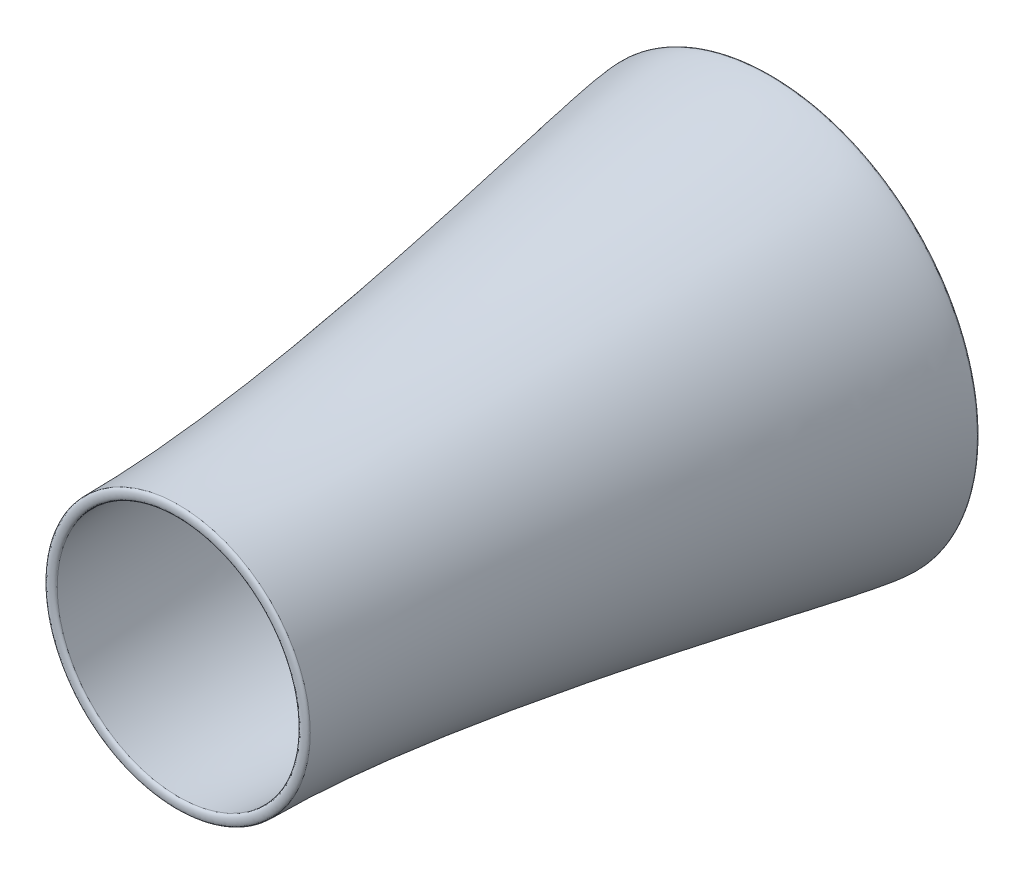
SolidWorks part; units mm, degrees
ref_plane "Front Plane" through (0, 0, 0) normal (0, 0, 1) x (1, 0, 0)
ref_plane "Top Plane" through (0, 0, 0) normal (0, 1, 0) x (1, 0, 0)
ref_plane "Right Plane" through (0, 0, 0) normal (1, 0, 0) x (0, 0, -1)
sketch "Sketch1" plane through (0, 0, 0) normal (0, 0, 1) x (1, 0, 0)
  circle A0 centre (0, 0) radius 50.8
  dimension "D1" = 101.6
ref_plane "Plane1" through (0, -254, 0) normal (0, 1, 0) x (1, 0, 0)
sketch "Sketch6" plane through (0, 0, 0) normal (0, 1, 0) x (1, 0, 0)
  line L0 (0, -99.6848) -> (0, 145.6048) construction
ref_plane "Plane2" through (0, -114.3, 0) normal (0, 1, 0) x (1, 0, 0)
sketch "Sketch12" plane through (0, 0, 0) normal (0, 1, 0) x (1, 0, 0)
  line L0 (0, -1104.7568) -> (0, -908.6135) construction
ref_plane "Plane3" through (0, 0, 203.2) normal (0, 0, 1) x (1, 0, 0)
ref_plane "Plane4" through (0, 0, 889) normal (0, 0, 1) x (1, 0, 0)
sketch "Sketch17" plane through (0, 0, 0) normal (0, 1, 0) x (1, 0, 0)
  line L0 (-259.4955, -43.5301) -> (-259.4955, 70.1436) construction
  line L1 (-110.6437, -1316.1124) -> (-110.6437, -853.5386) construction
  line L2 (-259.4955, 45.4622) -> (-387.328, 45.4622)
  line L3 (-387.328, 45.4622) -> (-387.328, -1084.8928)
  line L4 (-387.328, -1084.8928) -> (-110.6437, -1084.8928)
  spline S0 degree 3 poles (-259.4955, 45.4622) (-259.4955, -7.1736) (-207.7477, -105.8122) (-173.3147, -383.1384) (-92.4228, -818.9689) (-110.6437, -795.7842) (-110.6437, -1084.8928) knots 0 0 0 0 0.158009 0.206507 0.484977 1 1 1 1
sketch "Sketch21" plane through (0, 0, 0) normal (0, 1, 0) x (1, 0, 0)
  line L0 (-711.6099, -22.8536) -> (-711.6099, 113.778) construction
  line L1 (-450.1433, -1315.9117) -> (-450.1433, -853.874) construction
  line L2 (-622.1484, -0.8938) -> (-711.6099, -0.8938) construction
  line L3 (-414.4897, -2018.6594) -> (-450.1433, -2018.6594) construction
  line L4 (-414.4897, -2018.6594) -> (-450.1433, -2018.6594)
  line L6 (-622.1484, -0.8938) -> (-711.6099, -0.8938)
  spline S0 degree 3 poles (-622.1484, -0.8938) (-512.5874, -283.5588) (-414.9729, -786.3752) (-442.509, -1553.9603) (-414.4897, -2018.6594) knots 0 0 0 0 0.206507 1 1 1 1
  spline S1 degree 3 poles (-711.6099, -0.8938) (-711.6099, -126.2777) (-450.1433, -1288.3503) (-450.1433, -2018.6594) knots 0 0 0 0 1 1 1 1
  point P10 (-490.7044, -494.9814)
  point P11 (-570.9986, -443.7774)
  point P12 (-450.1433, -1074.8673)
  point P13 (-462.4277, -423.8357)
  point P14 (-385.8107, -2020.9984)
  point P15 (-441.2042, -1016.4054)
  point P16 (-414.4897, -2018.6594)
  point P17 (-484.9125, -450.8925)
revolve "Revolve2" add sketch "Sketch21" angle 360 about L0
sketch "Sketch22" plane through (0, 0, 0) normal (0, 1, 0) x (1, 0, 0)
  line L0 (-711.6099, -0.8938) -> (-622.1484, -0.8938)
  line L1 (-622.1484, -4.7028) -> (-622.1484, 2.9153) construction
  line L2 (-711.6099, 0.499) -> (-711.6099, -2.2865) construction
  spline S0 degree 3 poles (-711.6099, -0.8938) (-711.6099, 16.0396) (-622.1484, 16.0396) (-622.1484, -0.8938) knots 0 0 0 0 1 1 1 1
revolve "Revolve3" add sketch "Sketch22" angle 360 about L0
sketch "Sketch23" plane through (0, 0, 0) normal (0, 1, 0) x (1, 0, 0)
  line L0 (-450.1433, -2018.6594) -> (-414.4897, -2018.6594)
  line L1 (-450.1433, -2027.8705) -> (-450.1433, -2009.4483) construction
  line L2 (-414.4897, -2008.0864) -> (-414.4897, -2029.2324) construction
  spline S0 degree 3 poles (-450.1433, -2018.6594) (-450.1433, -2031.3594) (-414.4897, -2031.3594) (-414.4897, -2018.6594) knots 0 0 0 0 1 1 1 1
revolve "Revolve4" add sketch "Sketch23" angle 360 about L0
ref_plane "Plane5" through (289.9098, 0, 0) normal (1, 0, 0) x (0, 0, -1)
sketch "Sketch24" plane through (289.9098, 0, 0) normal (1, 0, 0) x (0, 0, -1)
  line L0 (-1123.5724, -17.6357) -> (119.2276, -17.6357) construction
  line L1 (-2018.6594, 0) -> (-0.8938, 0) construction
  line L2 (-2018.6594, -450.1433) -> (-2018.6594, 450.1433) construction
  line L3 (-0.8938, 711.6099) -> (-0.8938, -711.6099) construction
  text T0 "MD-130 Gas Turbine Engine" font "TI-Nspire" height in points 160
